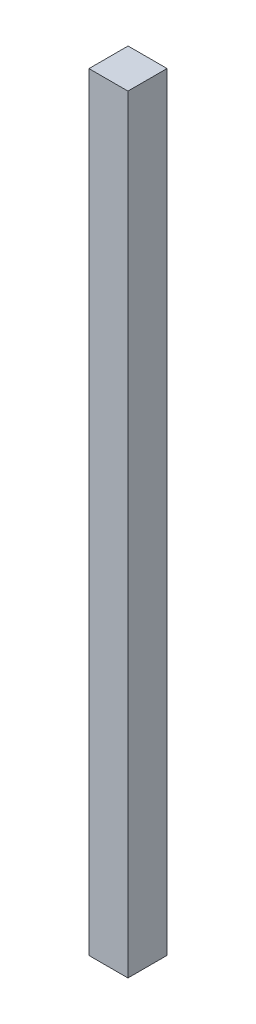
SolidWorks part; units mm, degrees
material "Cedar"
ref_plane "Front" through (0, 0, 0) normal (0, 0, 1) x (1, 0, 0)
ref_plane "Top" through (0, 0, 0) normal (0, 1, 0) x (1, 0, 0)
ref_plane "Right" through (0, 0, 0) normal (1, 0, 0) x (0, 0, -1)
sketch "Sketch1" plane through (0, 0, 0) normal (0, 1, 0) x (1, 0, 0)
  line L1 (-17.399, -17.4625) -> (17.399, -17.4625)
  line L2 (-17.399, -17.4625) -> (-17.399, 17.4625)
  line L3 (-17.399, 17.4625) -> (17.399, 17.4625)
  line L4 (17.399, -17.4625) -> (17.399, 17.4625)
  line L5 (-17.399, -17.4625) -> (17.399, 17.4625) construction
  line L6 (-17.399, 17.4625) -> (17.399, -17.4625) construction
  point P0 (0, 0)
  dimension "D1" = 34.925
  dimension "D2" = 34.798
extrude "Boss-Extrude1" add sketch "Sketch1" along normal blind 685.8 contours L1 L4 L3 L2
